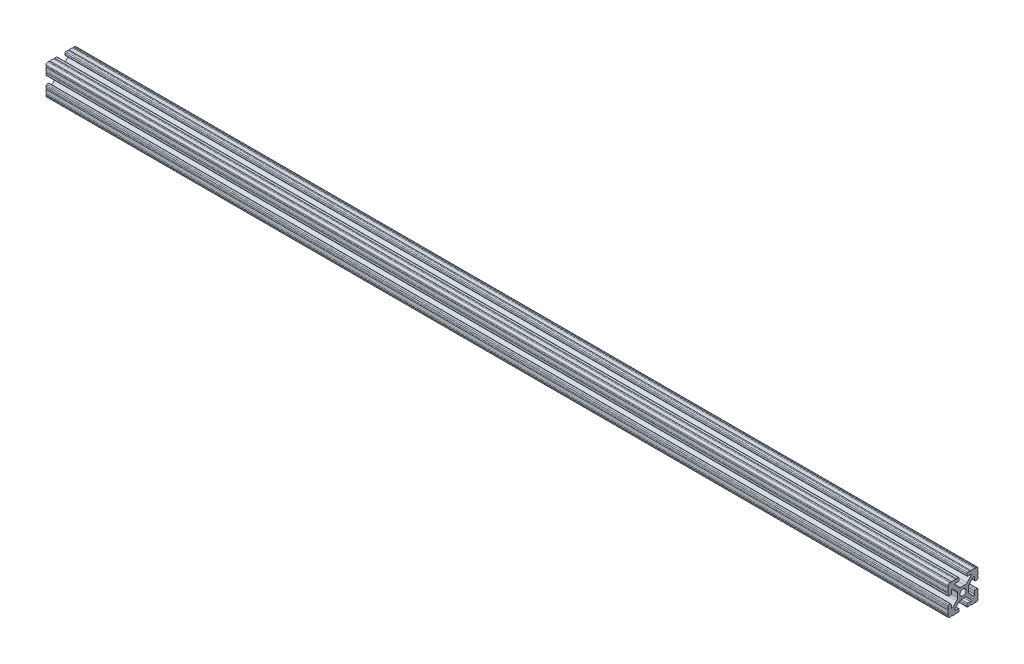
SolidWorks part; units mm, degrees
ref_plane "Front Plane" through (0, 0, 0) normal (0, 0, 1) x (1, 0, 0)
ref_plane "Top Plane" through (0, 0, 0) normal (0, 1, 0) x (1, 0, 0)
ref_plane "Right Plane" through (0, 0, 0) normal (1, 0, 0) x (0, 0, -1)
sketch "Sketch3"
sketch "Sketch2" plane through (0, 0, 0) normal (1, 0, 0) x (0, 0, -1)
  line L0 (16.1207, 7.3347) -> (19.544, 3.9114)
  line L1 (17.3256, 11.0651) -> (17.3256, 14.3349)
  line L2 (18.0653, 16.1207) -> (21.4886, 19.544)
  line L3 (22.598, 16.6362) -> (22.598, 19.0845)
  line L4 (24.7023, 15.9385) -> (23.2956, 15.9385)
  line L6 (2.1006, 25.4) -> (1.3474, 25.4)
  line L7 (16.6362, 2.802) -> (19.0845, 2.802)
  line L8 (0.6977, 15.9385) -> (2.1044, 15.9385)
  line L9 (2.802, 16.6362) -> (2.802, 19.0845)
  line L10 (0, 16.6362) -> (0, 18.2699)
  line L11 (8.0744, 11.0651) -> (8.0744, 14.3349)
  line L12 (7.3347, 16.1207) -> (3.9114, 19.544)
  line L13 (0, 19.2426) -> (0, 22.318)
  line L14 (0, 23.2994) -> (0, 24.0526)
  line L15 (6.1574, 25.4) -> (3.082, 25.4)
  line L16 (8.7638, 25.4) -> (7.1301, 25.4)
  line L17 (9.4615, 24.7023) -> (9.4615, 23.2956)
  line L18 (8.7638, 22.598) -> (6.3155, 22.598)
  line L19 (9.2793, 18.0653) -> (5.856, 21.4886)
  line L20 (14.3349, 17.3256) -> (11.0651, 17.3256)
  line L22 (25.4, 16.6362) -> (25.4, 18.2699)
  line L23 (25.4, 19.2426) -> (25.4, 22.318)
  line L24 (25.4, 23.2994) -> (25.4, 24.0526)
  line L25 (23.2994, 25.4) -> (24.0526, 25.4)
  line L26 (19.2426, 25.4) -> (22.318, 25.4)
  line L27 (16.6362, 25.4) -> (18.2699, 25.4)
  line L28 (15.9385, 24.7023) -> (15.9385, 23.2956)
  line L29 (16.6362, 22.598) -> (19.0845, 22.598)
  line L30 (16.1207, 18.0653) -> (19.544, 21.4886)
  line L31 (15.9385, 0.6977) -> (15.9385, 2.1044)
  line L32 (16.6362, 0) -> (18.2699, 0)
  line L33 (19.2426, 0) -> (22.318, 0)
  line L34 (23.2994, 0) -> (24.0526, 0)
  line L35 (25.4, 2.1006) -> (25.4, 1.3474)
  line L36 (25.4, 6.1574) -> (25.4, 3.082)
  line L37 (25.4, 8.7638) -> (25.4, 7.1301)
  line L38 (14.3349, 8.0744) -> (11.0651, 8.0744)
  line L39 (9.2793, 7.3347) -> (5.856, 3.9114)
  line L40 (8.7638, 2.802) -> (6.3155, 2.802)
  line L41 (9.4615, 0.6977) -> (9.4615, 2.1044)
  line L42 (8.7638, 0) -> (7.1301, 0)
  line L43 (6.1574, 0) -> (3.082, 0)
  line L44 (0, 2.1006) -> (0, 1.3474)
  line L45 (0, 6.1574) -> (0, 3.082)
  line L46 (7.3347, 9.2793) -> (3.9114, 5.856)
  line L47 (0, 8.7638) -> (0, 7.1301)
  line L48 (2.802, 8.7638) -> (2.802, 6.3155)
  line L49 (0.6977, 9.4615) -> (2.1044, 9.4615)
  line L50 (2.1006, 0) -> (1.3474, 0)
  line L51 (24.7023, 9.4615) -> (23.2956, 9.4615)
  line L52 (22.598, 8.7638) -> (22.598, 6.3155)
  line L53 (18.0653, 9.2793) -> (21.4886, 5.856)
  circle A0 centre (12.7, 12.7) radius 2.6035
  arc A1 (7.3347, 16.1207) -> (8.0744, 14.3349) centre (5.5489, 14.3349) cw
  arc A2 (2.802, 19.0845) -> (3.9114, 19.544) centre (3.4519, 19.0845) cw
  arc A3 (2.802, 16.6362) -> (2.1044, 15.9385) centre (2.1044, 16.6362) cw
  arc A4 (0, 16.6362) -> (0.6977, 15.9385) centre (0.6977, 16.6362) ccw
  arc A5 (-0.0204, 18.2642) -> (-0.0101, 19.2455) centre (-0.1467, 18.7562) ccw
  arc A6 (0, 22.318) -> (0, 23.2994) centre (-0.1315, 22.8087) ccw
  arc A7 (0, 24.0526) -> (1.3474, 25.4) centre (1.3474, 24.0526) cw
  arc A8 (3.082, 25.4) -> (2.1006, 25.4) centre (2.5913, 25.5315) cw
  arc A9 (7.1358, 25.4204) -> (6.1545, 25.4101) centre (6.6438, 25.5467) cw
  arc A10 (8.7638, 25.4) -> (9.4615, 24.7023) centre (8.7638, 24.7023) cw
  arc A11 (8.7638, 22.598) -> (9.4615, 23.2956) centre (8.7638, 23.2956) ccw
  arc A12 (6.3155, 22.598) -> (5.856, 21.4886) centre (6.3155, 21.9481) ccw
  arc A13 (9.2793, 18.0653) -> (11.0651, 17.3256) centre (11.0651, 19.8511) ccw
  arc A14 (18.0653, 16.1207) -> (17.3256, 14.3349) centre (19.8511, 14.3349) ccw
  arc A15 (22.598, 19.0845) -> (21.4886, 19.544) centre (21.9481, 19.0845) ccw
  arc A16 (22.598, 16.6362) -> (23.2956, 15.9385) centre (23.2956, 16.6362) ccw
  arc A17 (25.4, 16.6362) -> (24.7023, 15.9385) centre (24.7023, 16.6362) cw
  arc A18 (25.4204, 18.2642) -> (25.4101, 19.2455) centre (25.5467, 18.7562) cw
  arc A19 (25.4, 22.318) -> (25.4, 23.2994) centre (25.5315, 22.8087) cw
  arc A20 (25.4, 24.0526) -> (24.0526, 25.4) centre (24.0526, 24.0526) ccw
  arc A21 (22.318, 25.4) -> (23.2994, 25.4) centre (22.8087, 25.5315) ccw
  arc A22 (18.2642, 25.4204) -> (19.2455, 25.4101) centre (18.7562, 25.5467) ccw
  arc A23 (16.6362, 25.4) -> (15.9385, 24.7023) centre (16.6362, 24.7023) ccw
  arc A24 (16.6362, 22.598) -> (15.9385, 23.2956) centre (16.6362, 23.2956) cw
  arc A25 (19.0845, 22.598) -> (19.544, 21.4886) centre (19.0845, 21.9481) cw
  arc A26 (16.1207, 18.0653) -> (14.3349, 17.3256) centre (14.3349, 19.8511) cw
  arc A27 (16.1207, 7.3347) -> (14.3349, 8.0744) centre (14.3349, 5.5489) ccw
  arc A28 (19.0845, 2.802) -> (19.544, 3.9114) centre (19.0845, 3.4519) ccw
  arc A29 (16.6362, 2.802) -> (15.9385, 2.1044) centre (16.6362, 2.1044) ccw
  arc A30 (16.6362, 0) -> (15.9385, 0.6977) centre (16.6362, 0.6977) cw
  arc A31 (18.2642, -0.0204) -> (19.2455, -0.0101) centre (18.7562, -0.1467) cw
  arc A32 (22.318, 0) -> (23.2994, 0) centre (22.8087, -0.1315) cw
  arc A33 (25.4, 1.3474) -> (24.0526, 0) centre (24.0526, 1.3474) cw
  arc A34 (25.4, 3.082) -> (25.4, 2.1006) centre (25.5315, 2.5913) ccw
  arc A35 (25.4204, 7.1358) -> (25.4101, 6.1545) centre (25.5467, 6.6438) ccw
  arc A36 (25.4, 8.7638) -> (24.7023, 9.4615) centre (24.7023, 8.7638) ccw
  arc A37 (22.598, 8.7638) -> (23.2956, 9.4615) centre (23.2956, 8.7638) cw
  arc A38 (22.598, 6.3155) -> (21.4886, 5.856) centre (21.9481, 6.3155) cw
  arc A39 (18.0653, 9.2793) -> (17.3256, 11.0651) centre (19.8511, 11.0651) cw
  arc A40 (9.2793, 7.3347) -> (11.0651, 8.0744) centre (11.0651, 5.5489) cw
  arc A41 (6.3155, 2.802) -> (5.856, 3.9114) centre (6.3155, 3.4519) cw
  arc A42 (8.7638, 2.802) -> (9.4615, 2.1044) centre (8.7638, 2.1044) cw
  arc A43 (8.7638, 0) -> (9.4615, 0.6977) centre (8.7638, 0.6977) ccw
  arc A44 (7.1358, -0.0204) -> (6.1545, -0.0101) centre (6.6438, -0.1467) ccw
  arc A45 (3.082, 0) -> (2.1006, 0) centre (2.5913, -0.1315) ccw
  arc A46 (0, 1.3474) -> (1.3474, 0) centre (1.3474, 1.3474) ccw
  arc A47 (0, 3.082) -> (0, 2.1006) centre (-0.1315, 2.5913) cw
  arc A48 (-0.0204, 7.1358) -> (-0.0101, 6.1545) centre (-0.1467, 6.6438) cw
  arc A49 (0, 8.7638) -> (0.6977, 9.4615) centre (0.6977, 8.7638) cw
  arc A50 (2.802, 8.7638) -> (2.1044, 9.4615) centre (2.1044, 8.7638) ccw
  arc A51 (2.802, 6.3155) -> (3.9114, 5.856) centre (3.4519, 6.3155) ccw
  arc A52 (7.3347, 9.2793) -> (8.0744, 11.0651) centre (5.5489, 11.0651) ccw
  point P100 (12.7, 17.3256)
  point P181 (8.0744, 12.7)
  point P182 (17.3256, 12.7)
extrude "Boss-Extrude1" add sketch "Sketch2" along normal blind 762 contours A52 L46 A51 L48 A50 L49 A49 L47 A48 L45 A47 L44 A46 L50 A45 L43 A44 L42 A43 L41 A42 L40 A41 L39 A40 L38 A27 L0 A28 L7 A29 L31 A30 L32 A31 L33 A32 L34 A33 L35 A34 L36 A35 L37 A36 L51 A37 L52 A38 L53 A39
move or copy body "Body-Move/Copy1" bodies to move or copy 102 copy no translate (-150.0587, 28.7597, 59.645)
sketch "Sketch4" plane through (0, 0, 0) normal (0, 0, 1) x (1, 0, 0)
  line L0 (611.9413, 54.1597) -> (-150.0587, 54.1597) construction
  line L1 (-78.6761, 54.1597) -> (-106.0407, -11.9043)
  line L2 (378.5239, 54.1597) -> (405.8885, -11.9043)
  line L3 (405.8885, -11.9043) -> (480.3446, -42.745)
  line L4 (480.3446, -42.745) -> (535.2221, 89.7411)
  line L5 (535.2221, 89.7411) -> (378.5239, 89.7411)
  line L6 (378.5239, 89.7411) -> (378.5239, 54.1597)
  line L7 (-78.6761, 54.1597) -> (-78.6761, 92.6727)
  line L8 (-78.6761, 92.6727) -> (-197.9311, 43.2757)
  line L9 (-197.9311, 43.2757) -> (-164.965, -36.3115)
  line L10 (-164.965, -36.3115) -> (-106.0407, -11.9043)
  dimension "D1" = 67.5
  dimension "D2" = 67.5
